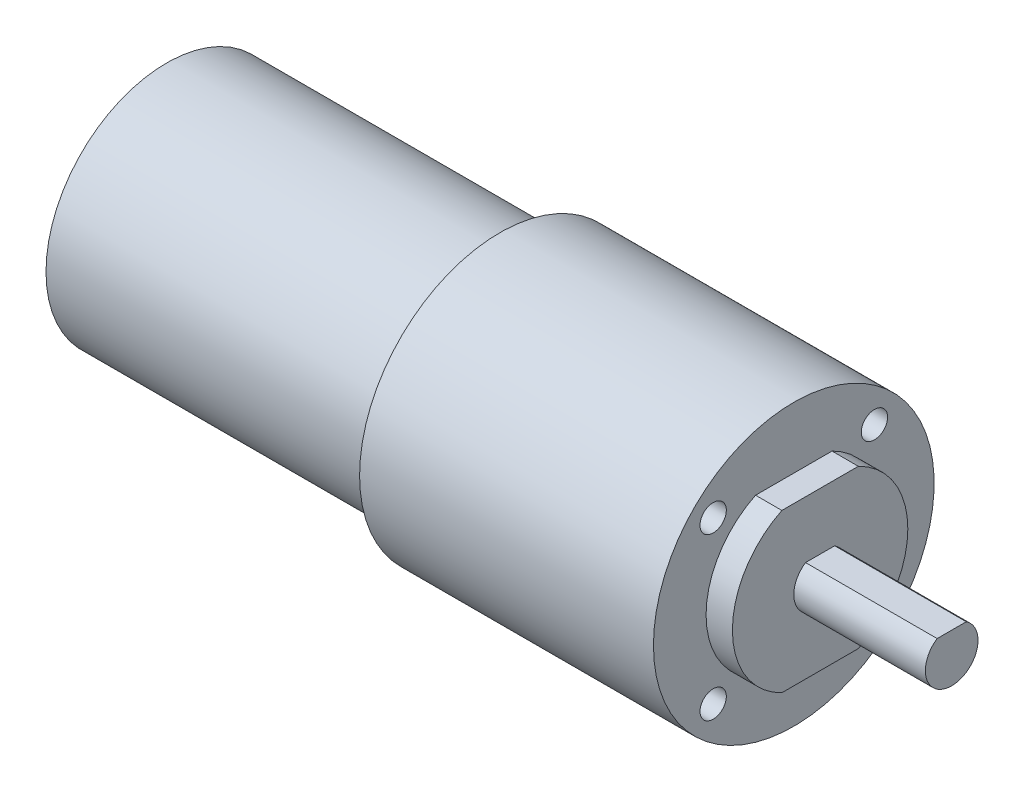
SolidWorks part; units mm, degrees
ref_plane "Front Plane" through (0, 0, 0) normal (0, 0, 1) x (1, 0, 0)
ref_plane "Top Plane" through (0, 0, 0) normal (0, 1, 0) x (1, 0, 0)
ref_plane "Right Plane" through (0, 0, 0) normal (1, 0, 0) x (0, 0, -1)
ref_axis "Axe1" through (-42.475, 0, 0) along (1, 0, 0)
sketch "Esquisse1" plane through (0, 0, 0) normal (0, 0, 1) x (1, 0, 0)
  line L0 (-38, 13.75) -> (0, 13.75)
  line L1 (0, 13.75) -> (0, 16)
  line L2 (0, 16) -> (33.5, 16)
  line L3 (33.5, 16) -> (33.5, 10)
  line L4 (33.5, 10) -> (36.5, 10)
  line L5 (36.5, 10) -> (36.5, 3)
  line L6 (36.5, 3) -> (51.5, 3)
  line L7 (51.5, 3) -> (51.5, 0)
  line L8 (51.5, 0) -> (-38, 0)
  line L9 (-38, 0) -> (-38, 13.75)
  dimension "D1" = 3
  dimension "D2" = 10
  dimension "D3" = 16
  dimension "D4" = 15
  dimension "D5" = 3
  dimension "D6" = 33.5
  dimension "D7" = 38
  dimension "D8" = 13.75
revolve "Révolution1" add sketch "Esquisse1" angle 360 about axis through (-42.475, 0, 0) along (1, 0, 0)
sketch "Esquisse2" plane through (36.5, 0, 0) normal (1, 0, 0) x (0, 0, -1)
  line L0 (-4.3589, 9) -> (4.3589, 9)
  line L1 (-4.3589, -9) -> (4.3589, -9)
  circle A0 centre (0, 0) radius 10 construction
  circle A1 centre (0, 0) radius 10 construction
  arc A2 (-4.3589, 9) -> (4.3589, 9) centre (0, 0) cw
  arc A3 (4.3589, -9) -> (-4.3589, -9) centre (0, 0) cw
  dimension "D1" = 9
  dimension "D2" = 9
extrude "MeplatFixing" cut sketch "Esquisse2" against normal up to surface (3 mm away) up to face at (33.5, 0, 16)
sketch "Esquisse3" plane through (51.5, 0, 0) normal (1, 0, 0) x (0, 0, -1)
  line L0 (-1.6583, 2.5) -> (1.6583, 2.5)
  circle A0 centre (0, 0) radius 3 construction
  arc A1 (-1.6583, 2.5) -> (1.6583, 2.5) centre (0, 0) cw
  dimension "D1" = 2.5
extrude "MeplatRotor" cut sketch "Esquisse3" against normal up to surface (15 mm away) up to face at (36.5, 0, 0)
sketch "Esquisse4" plane through (33.5, 0, 0) normal (1, 0, 0) x (0, 0, -1)
  line L0 (0, 0) -> (22.8047, 0) construction
  line L1 (0, 0) -> (9.1924, 9.1924) construction
  circle A0 centre (9.1924, 9.1924) radius 1.5
  dimension "D1" = 3
  dimension "D2" = 13
  dimension "D3" = 45
extrude "FixingHole" cut sketch "Esquisse4" against normal blind 5
pattern_circular "FixingHoleCircularRepetition" count 4 over 360 about axis through (0, 0, 0) along (1, 0, 0) of "FixingHole"
